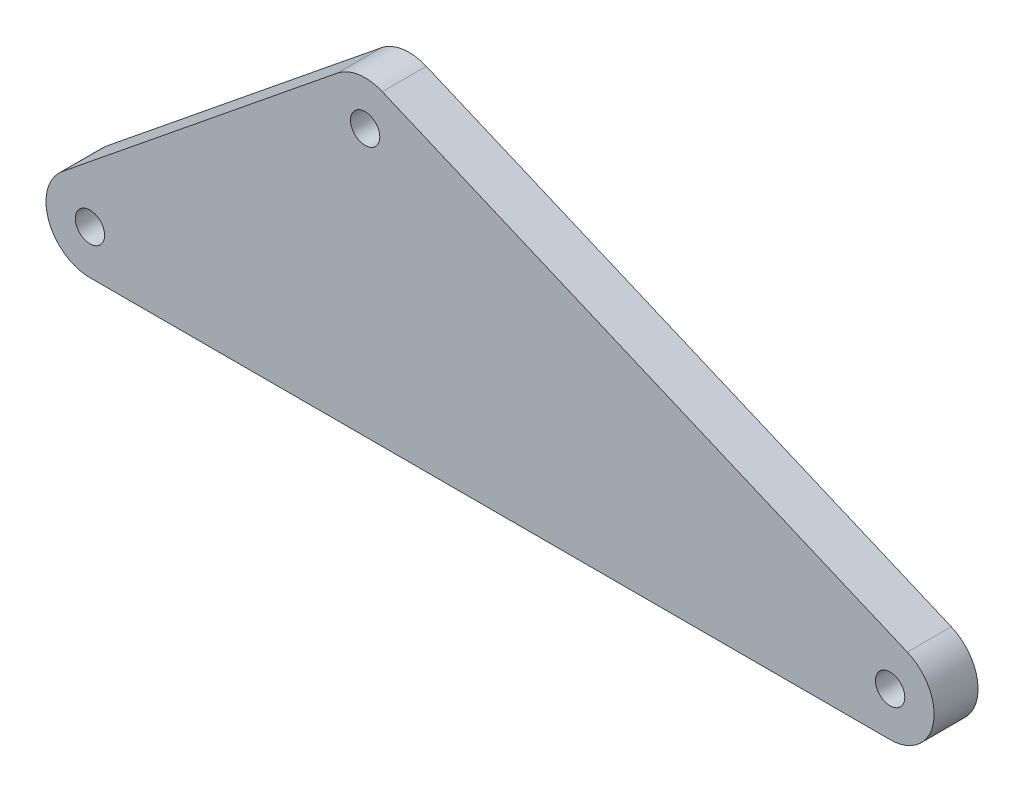
SolidWorks part; units mm, degrees
ref_plane "Спереди" through (0, 0, 0) normal (0, 0, 1) x (1, 0, 0)
ref_plane "Сверху" through (0, 0, 0) normal (0, 1, 0) x (1, 0, 0)
ref_plane "Справа" through (0, 0, 0) normal (1, 0, 0) x (0, 0, -1)
sketch "Эскиз1" plane through (0, 0, 0) normal (0, 0, 1) x (1, 0, 0)
  line L0 (-17.3575, -5.4234) -> (36.8251, 20.3496) construction
  line L1 (-2715.2651, -523.2425) -> (-2635.2651, -523.2425) construction
  line L2 (-40.1408, -46.1699) -> (39.8592, -46.1699) construction
  line L3 (-546, 0) -> (0, 0) construction
  line L4 (0, 0) -> (-358.2248, 152.0574) construction
  line L5 (-358.2248, 152.0574) -> (-546, 0) construction
  line L6 (-552.2932, 7.7715) -> (-364.518, 159.8288) construction
  line L7 (-354.3175, 161.2624) -> (3.9073, 9.205) construction
  line L8 (0, -10) -> (-546, -10) construction
  line L9 (-346.5028, 179.6725) -> (11.7219, 27.6151)
  line L10 (-564.8796, 23.3144) -> (-377.1044, 175.3718)
  line L11 (0, -30) -> (-546, -30)
  line L12 (0, 0) -> (-50000, 0) construction
  circle A0 centre (-546, 0) radius 10
  circle A1 centre (-358.2248, 152.0574) radius 10
  circle A2 centre (0, 0) radius 10
  arc A3 (-377.1044, 175.3718) -> (-346.5028, 179.6725) centre (-358.2248, 152.0574) cw
  arc A4 (11.7219, 27.6151) -> (0, -30) centre (0, 0) cw
  arc A5 (-546, -30) -> (-564.8796, 23.3144) centre (-546, 0) cw
  dimension "D4" = 20
  dimension "D5" = 20
  dimension "D6" = 546
  dimension "D1" = 60
  dimension "D2" = 80
  dimension "D3" = 80
  dimension "D7" = 39
  dimension "D8" = 118
extrude "Бобышка-Вытянуть1" add sketch "Эскиз1" along normal mid plane 30
sketch "Эскиз2" plane through (0, 0, -15) normal (0, 0, -1) x (-1, 0, 0)
  circle A1 centre (358.2248, 152.0574) radius 10 construction
  circle A2 centre (358.2248, 152.0574) radius 10 construction
  circle A3 centre (358.2248, 152.0574) radius 20
  dimension "D1" = 40
extrude "Вырез-Вытянуть1" cut sketch "Эскиз2" against normal blind 13
